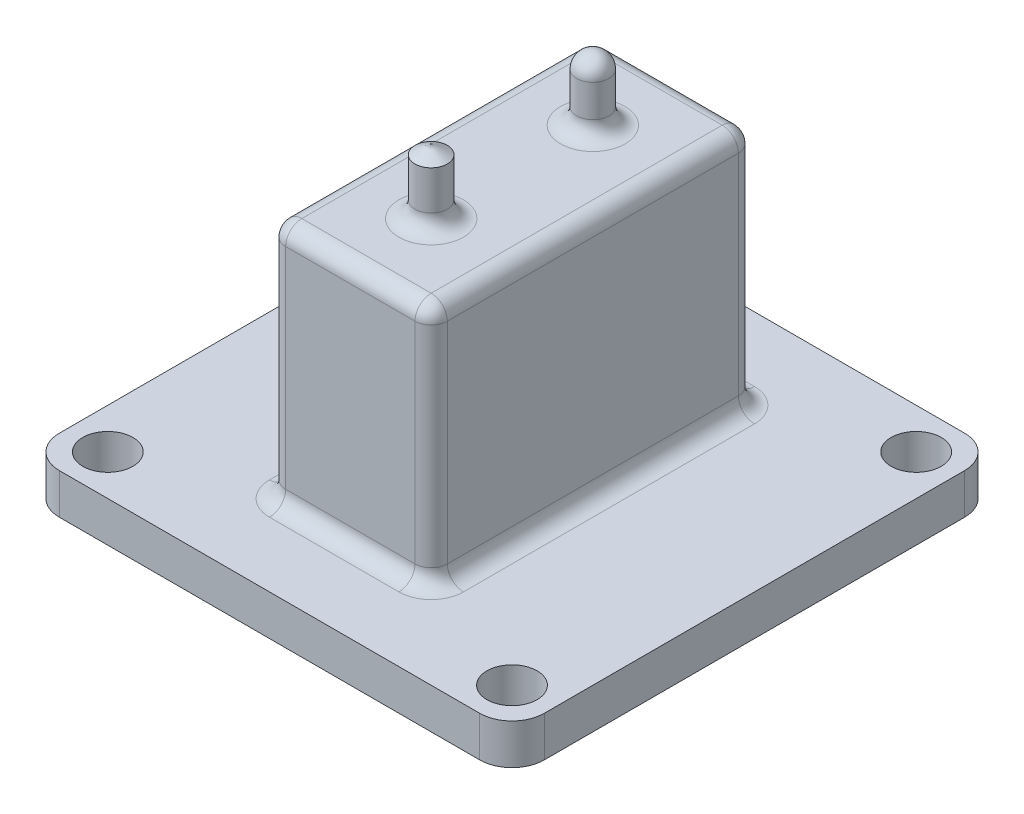
SolidWorks part; units mm, degrees
ref_plane "Front Plane" through (0, 0, 0) normal (0, 0, 1) x (1, 0, 0)
ref_plane "Top Plane" through (0, 0, 0) normal (0, 1, 0) x (1, 0, 0)
ref_plane "Right Plane" through (0, 0, 0) normal (1, 0, 0) x (0, 0, -1)
sketch "Sketch1" plane through (0, 0, 0) normal (0, 1, 0) x (1, 0, 0)
  line L1 (-30, -30) -> (30, -30)
  line L2 (-30, -30) -> (-30, 30)
  line L3 (-30, 30) -> (30, 30)
  line L4 (30, -30) -> (30, 30)
  line L5 (-30, -30) -> (30, 30) construction
  line L6 (-30, 30) -> (30, -30) construction
  circle A0 centre (-25, 25) radius 3.1
  circle A1 centre (-25, -25) radius 3.1
  circle A2 centre (25, -25) radius 3.1
  circle A3 centre (25, 25) radius 3.1
  point P0 (0, 0)
  dimension "D1" = 6.2
  dimension "D2" = 50
  dimension "D3" = 5
extrude "Boss-Extrude1" add sketch "Sketch1" along normal blind 5
sketch "Sketch4" plane through (0, 5, 0) normal (0, 1, 0) x (1, 0, 0)
  line L1 (-10, -20) -> (10, -20)
  line L2 (-10, -20) -> (-10, 20)
  line L3 (-10, 20) -> (10, 20)
  line L4 (10, -20) -> (10, 20)
  line L5 (-10, -20) -> (10, 20) construction
  line L6 (-10, 20) -> (10, -20) construction
  point P0 (0, 0)
  dimension "D1" = 40
  dimension "D2" = 20
extrude "Boss-Extrude3" add sketch "Sketch4" along normal blind 30
sketch "Sketch2" plane through (0, 35, 0) normal (0, 1, 0) x (1, 0, 0)
  line L0 (0, 10) -> (0, -10) construction
  circle A0 centre (0, 10) radius 2
  circle A1 centre (0, -10) radius 2
  point P3 (0, 0)
  dimension "D1" = 4
  dimension "D2" = 20
extrude "Boss-Extrude2" add sketch "Sketch2" along normal blind 8
fillet "Fillet1" radius 2 3 edges at (0, 43, -8) (0, 35, -12) (0, 35, 8)
fillet "Fillet2" radius 4 4 edges at (30, 2.5, -30) (-30, 2.5, -30) (-30, 2.5, 30) (30, 2.5, 30)
sketch "Sketch3" plane through (0, 0, 0) normal (1, 0, 0) x (0, 0, -1)
  line L1 (-8, 43) -> (-10, 43) construction
  line L2 (-10, 43) -> (-10, 44)
  line L5 (-10, 44) -> (-12, 44)
  line L8 (-10, 43) -> (-12, 41.8453)
  line L9 (-12, 41.8453) -> (-12, 44)
  line L10 (-10, 43) -> (-10, 11.5709) construction
  line L11 (-8, 43) -> (-12, 43) construction
  line L12 (-12, 43) -> (-12, 37) construction
  line L13 (-8, 37) -> (-8, 43) construction
  dimension "D1" = 60
  dimension "D2" = 1
revolve "Cut-Revolve3" cut sketch "Sketch3" angle 360 about L2
fillet "Fillet3" radius 2 12 edges at (10, 20, -20) (-10, 20, -20) (-10, 20, 20) (10, 20, 20) (0, 35, -20) (-10, 35, 0) (0, 35, 20) (10, 35, 0) (-10, 5, 0) (0, 5, -20) (0, 5, 20) (10, 5, 0)
